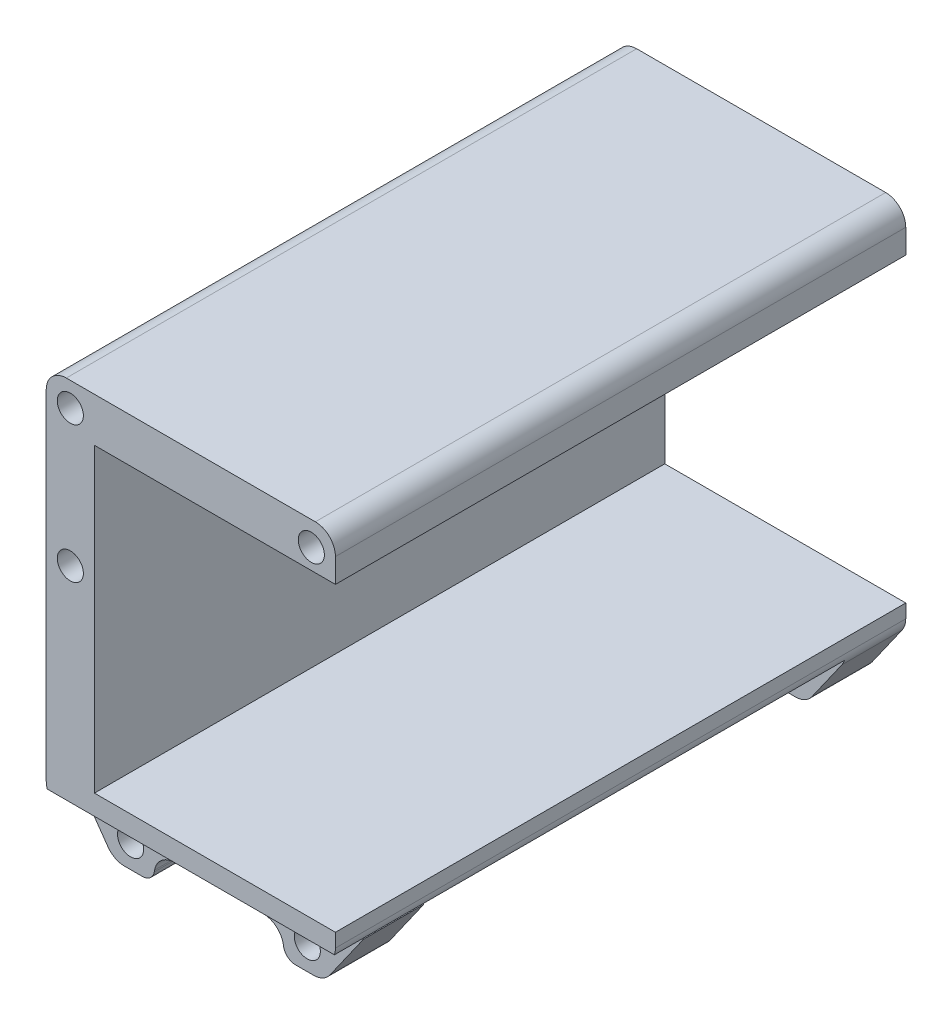
SolidWorks part; units mm, degrees
ref_plane "Plan de face" through (0, 0, 0) normal (0, 0, 1) x (1, 0, 0)
ref_plane "Plan de dessus" through (0, 0, 0) normal (0, 1, 0) x (1, 0, 0)
ref_plane "Plan de droite" through (0, 0, 0) normal (1, 0, 0) x (0, 0, -1)
sketch "Sketch1" plane through (0, 0, 0) normal (0, 0, 1) x (1, 0, 0)
  line L0 (36, 88.6593) -> (36, 99.6593)
  line L1 (36, 99.6593) -> (-31, 99.6593)
  line L4 (36, 10.243) -> (36, 13.6593)
  line L5 (36, 13.6593) -> (-24, 13.6593)
  line L6 (-24, 13.6593) -> (-24, 88.6593)
  line L7 (-24, 88.6593) -> (36, 88.6593)
  line L8 (36, 94.6593) -> (36, 8.6593) construction
  line L9 (-24, 51.6593) -> (-24, 88.6593) construction
  line L10 (-24, 88.6593) -> (24, 88.6593) construction
  line L11 (-31, 99.6593) -> (31, 99.6593) construction
  line L12 (24, 13.6593) -> (-24, 13.6593) construction
  line L27 (-36, 10.243) -> (-36, 94.6593) construction
  line L28 (-27.6363, -3.2193) -> (-35.0883, 7.3644) construction
  line L29 (-19.0484, -5.3407) -> (-23.5481, -5.3407) construction
  line L30 (-16.0166, -2.4397) -> (-16.0975, -2.8813) construction
  line L31 (11.0985, 1.6593) -> (-11.0985, 1.6593) construction
  line L32 (16.0975, -2.8813) -> (16.0166, -2.4397) construction
  line L33 (23.5481, -5.3407) -> (19.0484, -5.3407) construction
  line L34 (35.0883, 7.3644) -> (27.6363, -3.2193) construction
  line L35 (-36, 10.243) -> (-36, 94.6593)
  line L36 (-27.6363, -3.2193) -> (-35.0883, 7.3644)
  line L37 (-19.0484, -5.3407) -> (-23.5481, -5.3407)
  line L38 (-16.0166, -2.4397) -> (-16.0975, -2.8813)
  line L39 (11.0985, 1.6593) -> (-11.0985, 1.6593)
  line L40 (16.0975, -2.8813) -> (16.0166, -2.4397)
  line L41 (23.5481, -5.3407) -> (19.0484, -5.3407)
  line L42 (35.0883, 7.3644) -> (27.6363, -3.2193)
  circle A0 centre (30, 93.6593) radius 3.25
  circle A1 centre (-30, 93.6593) radius 3.25
  circle A2 centre (-30, 59.6593) radius 3.25
  circle A3 centre (30, 93.6593) radius 3.25 construction
  arc A20 (-31, 99.6593) -> (-36, 94.6593) centre (-31, 94.6593) ccw construction
  arc A21 (-36, 10.243) -> (-35.0883, 7.3644) centre (-31, 10.243) ccw construction
  arc A22 (-27.6363, -3.2193) -> (-23.5481, -5.3407) centre (-23.5481, -0.3407) ccw construction
  arc A23 (-19.0484, -5.3407) -> (-16.0975, -2.8813) centre (-19.0484, -2.3407) ccw construction
  arc A24 (-11.0985, 1.6593) -> (-16.0166, -2.4397) centre (-11.0985, -3.3407) ccw construction
  arc A25 (16.0166, -2.4397) -> (11.0985, 1.6593) centre (11.0985, -3.3407) ccw construction
  arc A26 (16.0975, -2.8813) -> (19.0484, -5.3407) centre (19.0484, -2.3407) ccw construction
  arc A27 (23.5481, -5.3407) -> (27.6363, -3.2193) centre (23.5481, -0.3407) ccw construction
  arc A28 (35.0883, 7.3644) -> (36, 10.243) centre (31, 10.243) ccw construction
  arc A29 (-31, 99.6593) -> (-36, 94.6593) centre (-31, 94.6593) ccw
  arc A30 (-36, 10.243) -> (-35.0883, 7.3644) centre (-31, 10.243) ccw
  arc A31 (-27.6363, -3.2193) -> (-23.5481, -5.3407) centre (-23.5481, -0.3407) ccw
  arc A32 (-19.0484, -5.3407) -> (-16.0975, -2.8813) centre (-19.0484, -2.3407) ccw
  arc A33 (-11.0985, 1.6593) -> (-16.0166, -2.4397) centre (-11.0985, -3.3407) ccw
  arc A34 (16.0166, -2.4397) -> (11.0985, 1.6593) centre (11.0985, -3.3407) ccw
  arc A35 (16.0975, -2.8813) -> (19.0484, -5.3407) centre (19.0484, -2.3407) ccw
  arc A36 (23.5481, -5.3407) -> (27.6363, -3.2193) centre (23.5481, -0.3407) ccw
  arc A37 (35.0883, 7.3644) -> (36, 10.243) centre (31, 10.243) ccw
  point P29 (30, 93.6593)
extrude "Boss-Extrude1" add sketch "Sketch1" along normal blind 142
sketch "Sketch2" plane through (-36, 0, 0) normal (-1, 0, 0) x (0, 0, 1)
  line L0 (15, -17.654) -> (142, -17.654)
  line L2 (142, -17.654) -> (142, 8.6593)
  line L3 (142, 99.6593) -> (142, 10.243) construction
  line L4 (142, 8.6593) -> (15, 8.6593)
  line L5 (15, 8.6593) -> (15, -17.654)
  line L6 (142, 13.6593) -> (0, 13.6593) construction
  line L7 (0, 10.243) -> (0, 13.6593) construction
  point P2 (15, 1.6593)
  point P3 (145.4191, -17.654)
  dimension "D1" = 5
  dimension "D2" = 15
extrude "Cut-Extrude1" cut sketch "Sketch2" against normal through all
fillet "Fillet1" radius 5 1 edges at (36, 99.6593, 71)
sketch "Sketch3" plane through (0, 0, 120) normal (0, 0, 1) x (1, 0, 0)
  line L0 (-36, 8.6593) -> (-27.6363, -3.2193)
  line L1 (-36, 8.6593) -> (36, 8.6593)
  line L2 (36, 8.6593) -> (27.6363, -3.2193)
  line L3 (23.5481, -5.3407) -> (19.0484, -5.3407) construction
  line L4 (23.5481, -5.3407) -> (19.0484, -5.3407)
  line L5 (-23.5481, -5.3407) -> (-19.0484, -5.3407) construction
  line L6 (-23.5481, -5.3407) -> (-19.0484, -5.3407)
  line L7 (-11.0985, 1.6593) -> (11.0985, 1.6593) construction
  line L8 (-11.0985, 1.6593) -> (11.0985, 1.6593)
  line L9 (-16.0975, -2.8813) -> (-16.0166, -2.4397) construction
  line L10 (16.0975, -2.8813) -> (16.0166, -2.4397) construction
  line L11 (-16.0975, -2.8813) -> (-16.0166, -2.4397)
  line L12 (16.0975, -2.8813) -> (16.0166, -2.4397)
  line L13 (-36, 94.6593) -> (-36, 10.243) construction
  line L14 (35.7426, 8.6593) -> (-35.7426, 8.6593) construction
  circle A0 centre (-22, 0.6593) radius 3.25 construction
  circle A1 centre (22, 0.6593) radius 3.25 construction
  circle A2 centre (-22, 0.6593) radius 3.25
  circle A3 centre (22, 0.6593) radius 3.25
  arc A4 (-28.5481, -0.3407) -> (-23.5481, -5.3407) centre (-23.5481, -0.3407) ccw construction
  arc A5 (23.5481, -5.3407) -> (28.5481, -0.3407) centre (23.5481, -0.3407) ccw construction
  arc A6 (-27.6363, -3.2193) -> (-23.5481, -5.3407) centre (-23.5481, -0.3407) ccw
  arc A7 (23.5481, -5.3407) -> (27.6363, -3.2193) centre (23.5481, -0.3407) ccw
  arc A8 (16.0975, -2.8813) -> (19.0484, -5.3407) centre (19.0484, -2.3407) ccw construction
  arc A9 (16.0975, -2.8813) -> (19.0484, -5.3407) centre (19.0484, -2.3407) ccw
  arc A10 (-19.0484, -5.3407) -> (-16.0975, -2.8813) centre (-19.0484, -2.3407) ccw construction
  arc A11 (-19.0484, -5.3407) -> (-16.0975, -2.8813) centre (-19.0484, -2.3407) ccw
  arc A12 (-11.0985, 1.6593) -> (-16.0166, -2.4397) centre (-11.0985, -3.3407) ccw construction
  arc A13 (16.0166, -2.4397) -> (11.0985, 1.6593) centre (11.0985, -3.3407) ccw construction
  arc A14 (-11.0985, 1.6593) -> (-16.0166, -2.4397) centre (-11.0985, -3.3407) ccw
  arc A15 (16.0166, -2.4397) -> (11.0985, 1.6593) centre (11.0985, -3.3407) ccw
  point P11 (28.1052, -2.398)
  point P28 (0, 0)
  point P32 (0, 0)
  point P35 (-36, 4.6083)
extrude "Boss-Extrude2" add sketch "Sketch3" along normal blind 15
